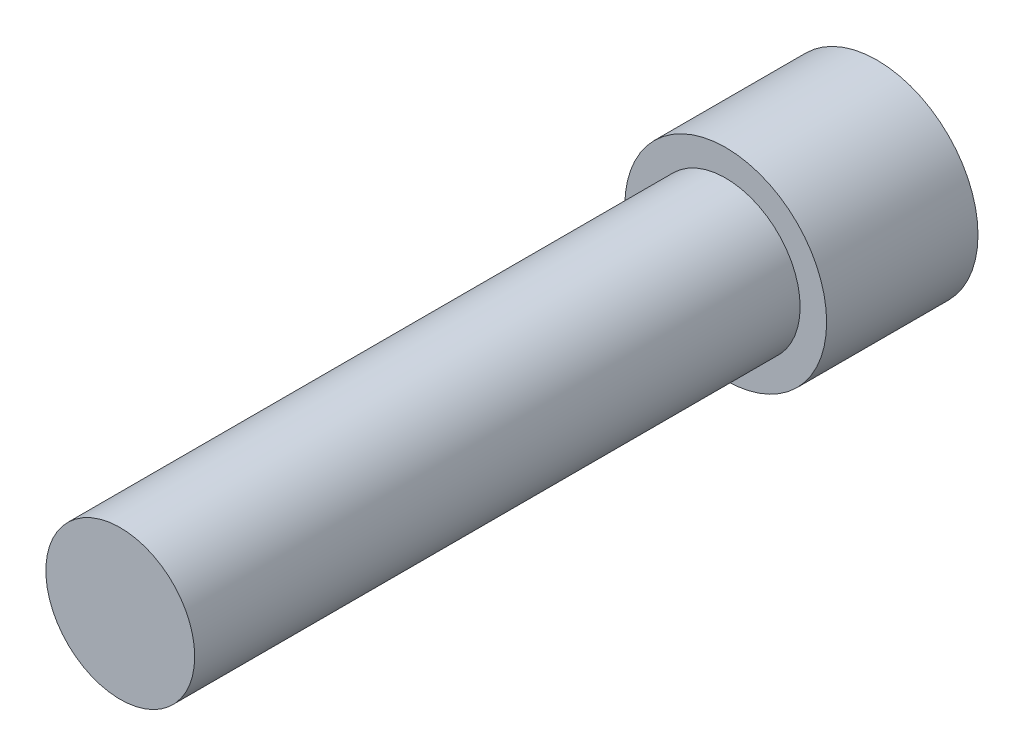
SolidWorks part; units mm, degrees
ref_plane "Front Plane" through (0, 0, 0) normal (0, 0, 1) x (1, 0, 0)
ref_plane "Top Plane" through (0, 0, 0) normal (0, 1, 0) x (1, 0, 0)
ref_plane "Right Plane" through (0, 0, 0) normal (1, 0, 0) x (0, 0, -1)
sketch "Sketch1" plane through (0, 0, 0) normal (0, 0, 1) x (1, 0, 0)
  circle A0 centre (0, 0) radius 2
extrude "Extrude1" add sketch "Sketch1" along normal blind 3
sketch "Sketch3" plane through (0, 0, 0) normal (0, 0, -1) x (-1, 0, 0)
  line L1 (-1.4434, 0) -> (-0.7217, -1.25)
  line L2 (-0.7217, -1.25) -> (0.7217, -1.25)
  line L3 (0.7217, -1.25) -> (1.4434, 0)
  line L4 (1.4434, 0) -> (0.7217, 1.25)
  line L5 (0.7217, 1.25) -> (-0.7217, 1.25)
  line L6 (-0.7217, 1.25) -> (-1.4434, 0)
  circle A0 centre (0, 0) radius 1.25 construction
extrude "Extrude3" cut sketch "Sketch3" against normal blind 1.82
sketch "Sketch2" plane through (0, 0, 3) normal (0, 0, 1) x (1, 0, 0)
  circle A0 centre (0, 0) radius 1.475
extrude "Extrude2" add sketch "Sketch2" along normal blind 12
